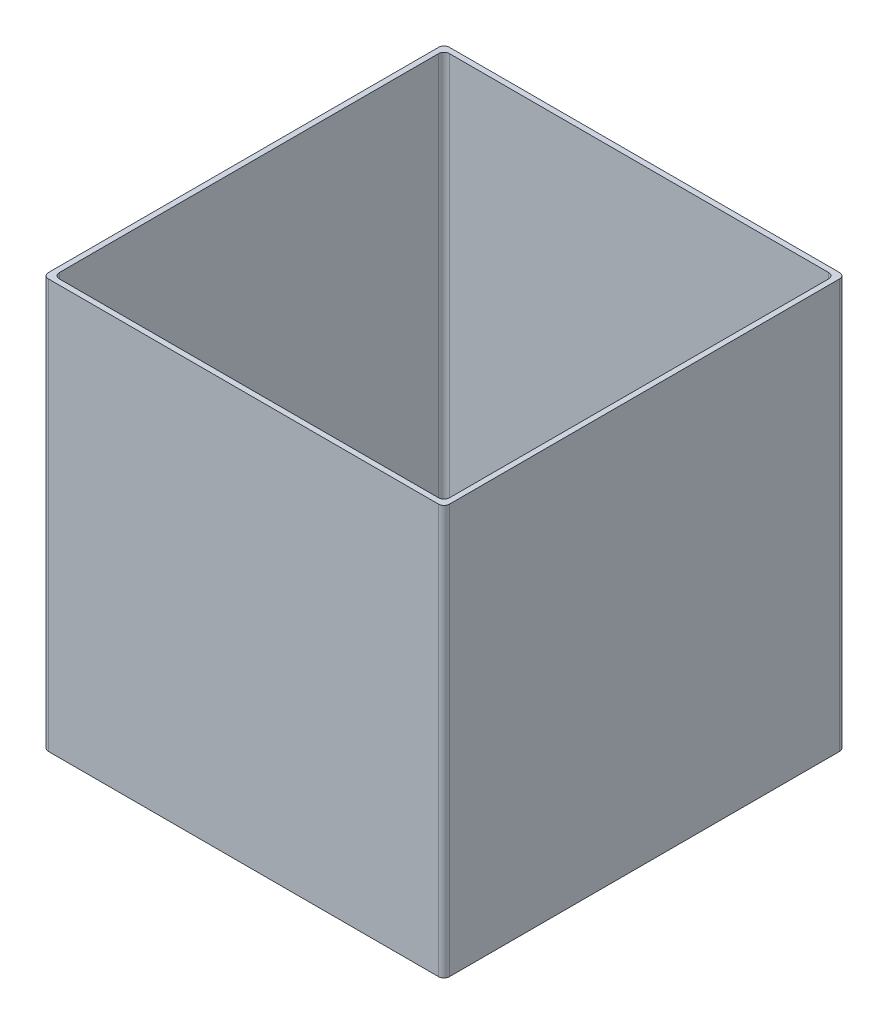
SolidWorks part; units mm, degrees
material "Акрил (Средняя-высокая ударопрочность)"
ref_plane "Спереди" through (0, 0, 0) normal (0, 0, 1) x (1, 0, 0)
ref_plane "Сверху" through (0, 0, 0) normal (0, 1, 0) x (1, 0, 0)
ref_plane "Справа" through (0, 0, 0) normal (1, 0, 0) x (0, 0, -1)
sketch "Эскиз1" plane through (0, 0, 0) normal (0, 1, 0) x (1, 0, 0)
  line L1 (2, 0) -> (145, 0)
  line L2 (0, 2) -> (0, 145)
  line L3 (2, 147) -> (145, 147)
  line L4 (147, 2) -> (147, 145)
  line L5 (4, 145) -> (143, 145)
  line L6 (2, 143) -> (2, 4)
  line L7 (4, 2) -> (143, 2)
  line L8 (145, 143) -> (145, 4)
  arc A0 (0, 145) -> (2, 147) centre (2, 145) cw
  arc A1 (4, 145) -> (2, 143) centre (4, 143) ccw
  arc A2 (145, 147) -> (147, 145) centre (145, 145) cw
  arc A3 (143, 145) -> (145, 143) centre (143, 143) cw
  arc A4 (145, 0) -> (147, 2) centre (145, 2) ccw
  arc A5 (143, 2) -> (145, 4) centre (143, 4) ccw
  arc A6 (2, 0) -> (0, 2) centre (2, 2) cw
  arc A7 (2, 4) -> (4, 2) centre (4, 4) ccw
  point P11 (0, 147)
  point P20 (147, 0)
  point P25 (0, 0)
  dimension "D7" = 2
  dimension "D1" = 147
  dimension "D2" = 147
  dimension "D3" = 2
  dimension "D4" = 2
  dimension "D5" = 2
  dimension "D6" = 2
extrude "Бобышка-Вытянуть1" add sketch "Эскиз1" along normal blind 150
